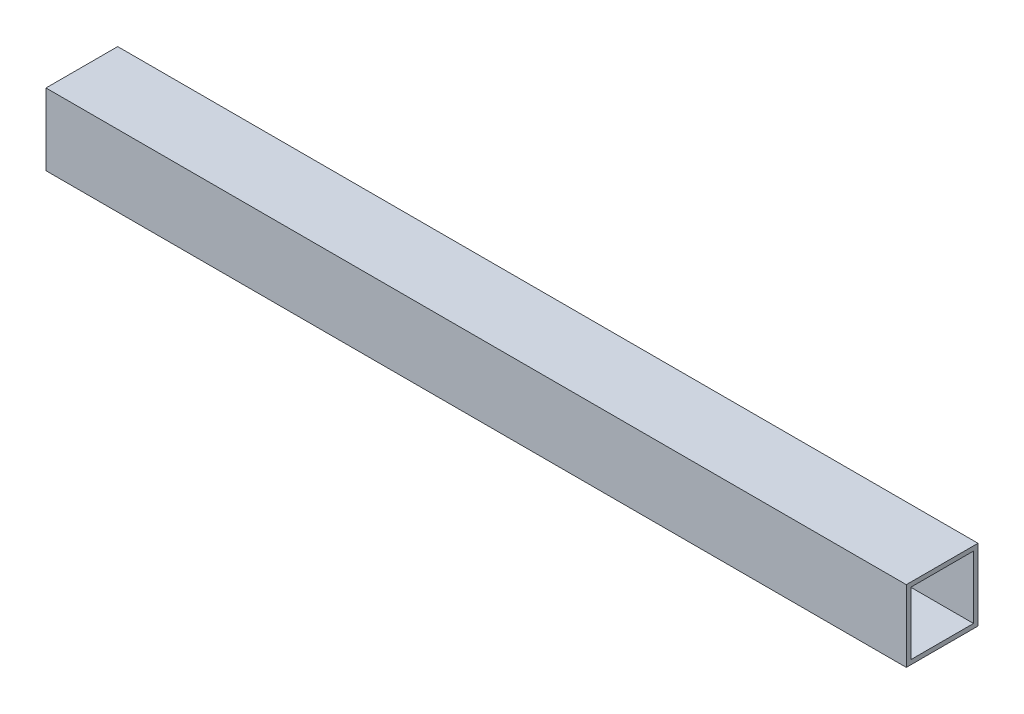
SolidWorks part; units mm, degrees
ref_plane "Front Plane" through (0, 0, 0) normal (0, 0, 1) x (1, 0, 0)
ref_plane "Top Plane" through (0, 0, 0) normal (0, 1, 0) x (1, 0, 0)
ref_plane "Right Plane" through (0, 0, 0) normal (1, 0, 0) x (0, 0, -1)
sketch "Sketch2" plane through (0, 0, 0) normal (1, 0, 0) x (0, 0, -1)
  line L1 (-12.7, 12.7) -> (12.7, 12.7)
  line L2 (-12.7, 12.7) -> (-12.7, -12.7)
  line L3 (-12.7, -12.7) -> (12.7, -12.7)
  line L4 (12.7, 12.7) -> (12.7, -12.7)
  line L5 (-12.7, 12.7) -> (12.7, -12.7) construction
  line L6 (-12.7, -12.7) -> (12.7, 12.7) construction
  point P0 (0, 0)
  dimension "D1" = 25.4
  dimension "D2" = 25.4
extrude "Extrude-Thin1" add sketch "Sketch2" along normal blind 304.8 thin
